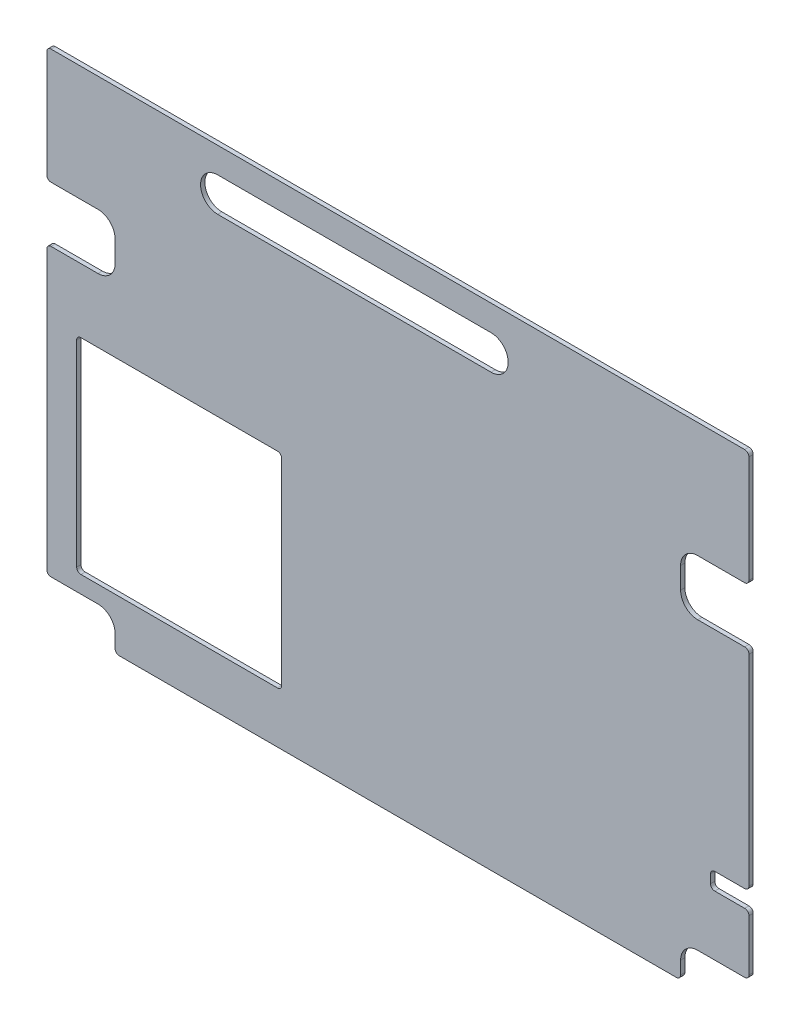
SolidWorks part; units mm, degrees
material "PC High Viscosity"
ref_plane "Front Plane" through (0, 0, 0) normal (0, 0, 1) x (1, 0, 0)
ref_plane "Top Plane" through (0, 0, 0) normal (0, 1, 0) x (1, 0, 0)
ref_plane "Right Plane" through (0, 0, 0) normal (1, 0, 0) x (0, 0, -1)
sketch "Sketch1" plane through (0, 0, 0) normal (0, 0, 1) x (1, 0, 0)
  line L1 (0, 0) -> (1043.686, 0)
  line L2 (0, 0) -> (0, 730.25)
  line L3 (0, 730.25) -> (1043.686, 730.25)
  line L4 (1043.686, 0) -> (1043.686, 730.25)
  dimension "D1" = 1043.686
  dimension "D2" = 730.25
extrude "Boss-Extrude1" add sketch "Sketch1" along normal blind 6.35
sketch "Sketch9" plane through (0, 0, 0) normal (0, 0, -1) x (-1, 0, 0)
  line L0 (0, 730.25) -> (0, 0) construction
  line L1 (-349.25, 381) -> (-44.45, 381)
  line L2 (-349.25, 381) -> (-349.25, 76.2)
  line L3 (-349.25, 76.2) -> (-44.45, 76.2)
  line L4 (-44.45, 381) -> (-44.45, 76.2)
  line L5 (0, 0) -> (-1043.686, 0) construction
  dimension "D1" = 44.45
  dimension "D2" = 76.2
  dimension "D3" = 304.8
  dimension "D4" = 304.8
extrude "Cut-Extrude3" cut sketch "Sketch9" against normal blind 6.35
sketch "Sketch10" plane through (0, 0, 6.35) normal (0, 0, 1) x (1, 0, 0)
  line L0 (0, 730.25) -> (0, 0) construction
  line L1 (0, 0) -> (1043.686, 0) construction
  line L2 (1043.686, 0) -> (1043.686, 730.25) construction
  line L3 (76.2, 50.8) -> (0, 50.8)
  line L4 (0, 50.8) -> (0, 0)
  line L6 (101.6, 25.4) -> (101.6, 0)
  line L7 (101.6, 0) -> (0, 0)
  line L8 (942.086, 25.4) -> (942.086, 0)
  line L9 (942.086, 0) -> (1043.686, 0)
  line L10 (967.486, 50.8) -> (1043.686, 50.8)
  line L11 (1043.686, 50.8) -> (1043.686, 0)
  line L12 (967.486, 558.8) -> (1043.686, 558.8)
  line L13 (1043.686, 558.8) -> (1043.686, 476.25)
  line L14 (1043.686, 476.25) -> (967.486, 476.25)
  line L15 (942.086, 533.4) -> (942.086, 501.65)
  line L16 (1043.686, 0) -> (1043.686, 730.25) construction
  line L17 (76.2, 558.8) -> (0, 558.8)
  line L18 (0, 558.8) -> (0, 476.25)
  line L19 (0, 476.25) -> (76.2, 476.25)
  line L20 (101.6, 501.65) -> (101.6, 533.4)
  line L21 (0, 730.25) -> (0, 0) construction
  line L22 (1043.686, 139.7) -> (1043.686, 165.1)
  line L23 (1043.686, 139.7) -> (992.886, 139.7)
  line L24 (1043.686, 165.1) -> (992.886, 165.1)
  line L25 (986.536, 146.05) -> (986.536, 158.75)
  line L30 (0, 0) -> (1043.686, 0) construction
  arc A0 (101.6, 533.4) -> (76.2, 558.8) centre (76.2, 533.4) ccw
  arc A1 (101.6, 25.4) -> (76.2, 50.8) centre (76.2, 25.4) ccw
  arc A2 (967.486, 558.8) -> (942.086, 533.4) centre (967.486, 533.4) ccw
  arc A3 (967.486, 50.8) -> (942.086, 25.4) centre (967.486, 25.4) ccw
  arc A4 (967.486, 476.25) -> (942.086, 501.65) centre (967.486, 501.65) cw
  arc A5 (76.2, 476.25) -> (101.6, 501.65) centre (76.2, 501.65) ccw
  arc A6 (986.536, 146.05) -> (992.886, 139.7) centre (992.886, 146.05) ccw
  arc A7 (986.536, 158.75) -> (992.886, 165.1) centre (992.886, 158.75) cw
  point P32 (942.086, 517.525)
  point P47 (986.536, 152.4)
  point P52 (986.536, 165.1)
  dimension "D1" = 50.8
  dimension "D2" = 76.2
  dimension "D7" = 25.4
  dimension "D10" = 25.4
  dimension "D14" = 6.35
  dimension "D3" = 508
  dimension "D4" = 25.4
  dimension "D5" = 508
  dimension "D6" = 76.2
  dimension "D8" = 82.55
  dimension "D9" = 101.6
  dimension "D11" = 152.4
  dimension "D12" = 25.4
  dimension "D13" = 57.15
extrude "Cut-Extrude4" cut sketch "Sketch10" against normal blind 6.35
fillet "Fillet1" radius 6.35 16 edges at (44.45, 381, 3.175) (349.25, 381, 3.175) (349.25, 76.2, 3.175) (44.45, 76.2, 3.175) (101.6, 0, 3.175) (0, 50.8, 3.175) (0, 730.25, 3.175) (1043.686, 730.25, 3.175) (1043.686, 50.8, 3.175) (942.086, 0, 3.175) (0, 476.25, 3.175) (0, 558.8, 3.175) (1043.686, 139.7, 3.175) (1043.686, 165.1, 3.175) (1043.686, 476.25, 3.175) (1043.686, 558.8, 3.175)
sketch "Sketch14" plane through (0, 0, 0) normal (0, 0, -1) x (-1, 0, 0)
  line L0 (-660.4, 666.75) -> (-254, 666.75) construction
  line L1 (-660.4, 692.15) -> (-254, 692.15)
  line L2 (-660.4, 641.35) -> (-254, 641.35)
  line L3 (-1037.336, 730.25) -> (-6.35, 730.25) construction
  line L4 (0, 723.9) -> (0, 558.8) construction
  arc A0 (-660.4, 692.15) -> (-660.4, 641.35) centre (-660.4, 666.75) ccw
  arc A1 (-254, 641.35) -> (-254, 692.15) centre (-254, 666.75) ccw
  point P2 (-457.2, 666.75)
  dimension "D1" = 63.5
  dimension "D2" = 406.4
  dimension "D3" = 50.8
  dimension "D4" = 457.2
extrude "Cut-Extrude6" cut sketch "Sketch14" against normal through all
